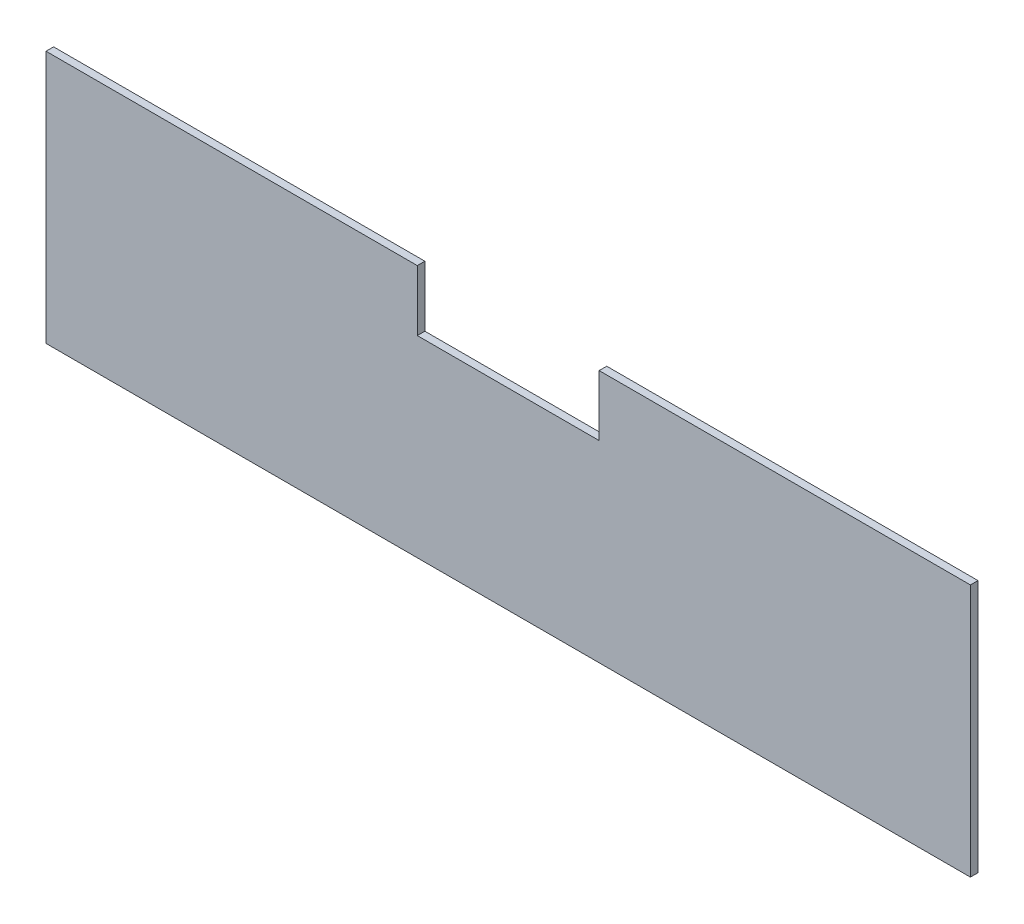
SolidWorks part; units mm, degrees
ref_plane "Front" through (0, 0, 0) normal (0, 0, 1) x (1, 0, 0)
ref_plane "Top" through (0, 0, 0) normal (0, 1, 0) x (1, 0, 0)
ref_plane "Right" through (0, 0, 0) normal (1, 0, 0) x (0, 0, -1)
sketch "Sketch1" plane through (0, 0, 0) normal (0, 0, 1) x (1, 0, 0)
  line L0 (38.1, 53.0225) -> (193.675, 53.0225)
  line L1 (-193.675, 53.0225) -> (-38.1, 53.0225)
  line L2 (-193.675, 53.0225) -> (-193.675, -53.0225)
  line L3 (-193.675, -53.0225) -> (193.675, -53.0225)
  line L4 (193.675, 53.0225) -> (193.675, -53.0225)
  line L6 (-38.1, 53.0225) -> (-38.1, 27.6225)
  line L7 (-38.1, 27.6225) -> (38.1, 27.6225)
  line L8 (38.1, 53.0225) -> (38.1, 27.6225)
  point P4 (0, -53.0225)
  point P6 (-193.675, 0)
  point P11 (0, 27.6225)
  dimension "D1" = 387.35
  dimension "D2" = 106.045
  dimension "D3" = 76.2
  dimension "D4" = 25.4
extrude "Boss-Extrude1" add sketch "Sketch1" along normal blind 3.175
